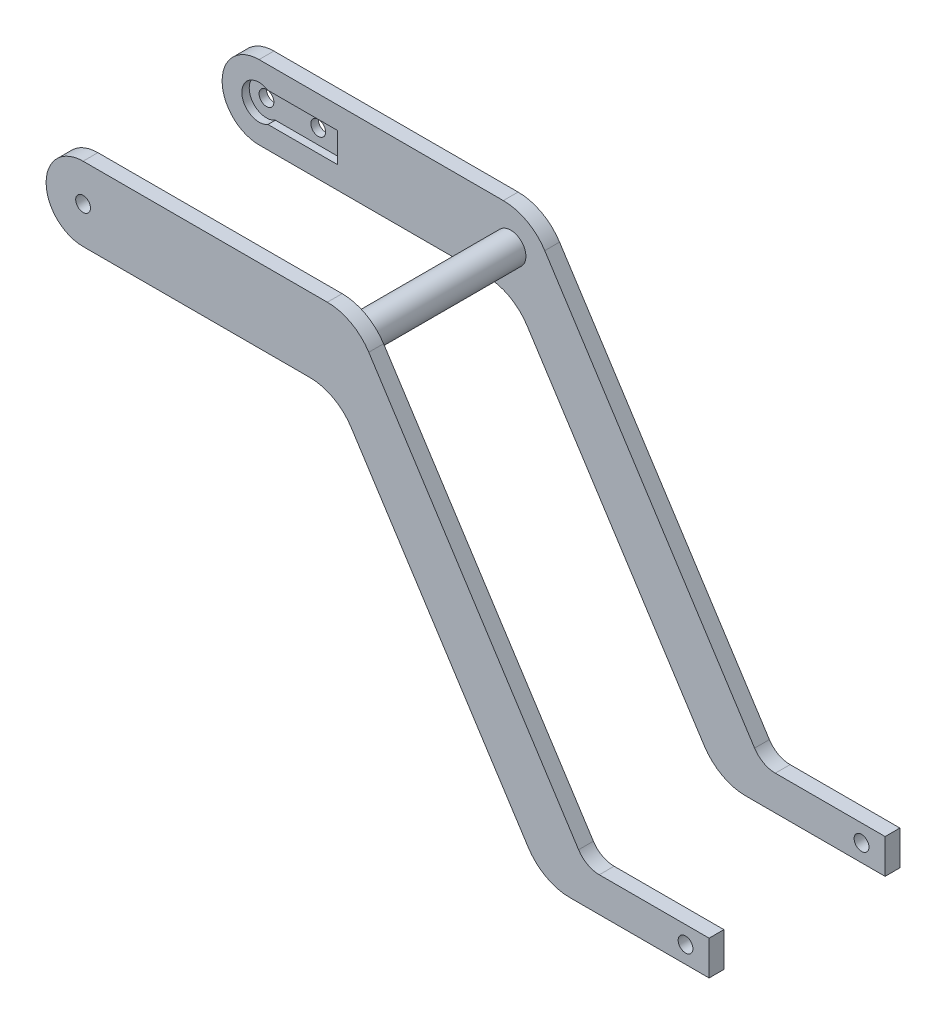
SolidWorks part; units mm, degrees
ref_plane "前基準面" through (0, 0, 0) normal (0, 0, 1) x (1, 0, 0)
ref_plane "上基準面" through (0, 0, 0) normal (0, 1, 0) x (1, 0, 0)
ref_plane "右基準面" through (0, 0, 0) normal (1, 0, 0) x (0, 0, -1)
sketch "草?" plane through (0, 0, 0) normal (0, 0, 1) x (1, 0, 0)
  line L0 (0, 0) -> (-0.115, 0)
  line L1 (0, -15) -> (2.1689, -15)
  line L3 (0, 0) -> (49.5442, 0)
  line L4 (2.1689, -15) -> (45.9764, -15)
  line L5 (54.3851, -19.5877) -> (90.317, -75.4123)
  line L6 (57.9529, -4.5877) -> (100.5105, -70.7062)
  line L7 (98.7257, -80) -> (126.9869, -80)
  line L8 (104.7148, -73) -> (126.9869, -73)
  line L9 (126.9869, -73) -> (126.9869, -80)
  arc A0 (0, 0) -> (0, -15) centre (0, -7.5) ccw
  arc A1 (49.5442, 0) -> (57.9529, -4.5877) centre (49.5442, -10) cw
  arc A2 (45.9764, -15) -> (54.3851, -19.5877) centre (45.9764, -25) cw
  arc A3 (90.317, -75.4123) -> (98.7257, -80) centre (98.7257, -70) ccw
  arc A4 (100.5105, -70.7062) -> (104.7148, -73) centre (104.7148, -68) ccw
  circle A5 centre (0, -7.5) radius 1.5
  point P13 (55, 0)
  point P22 (101.9869, -73)
  dimension "D1" = 15
  dimension "D2" = 3
  dimension "D6" = 10
  dimension "D7" = 10
  dimension "D8" = 10
  dimension "D9" = 5
  dimension "D3" = 55
  dimension "D4" = 25
  dimension "D5" = 7
  dimension "D10" = 65
extrude "填料-伸長1" add sketch "草?" along normal blind 3 contours A4 L6 A1 L3 A0 L1 L4 A2 L5 A3 L7 L9 L8 A5
sketch "草圖2" plane through (0, 0, 3) normal (0, 0, 1) x (1, 0, 0)
  line L0 (126.9869, -73) -> (126.9869, -80) construction
  circle A0 centre (122.2069, -76.5) radius 1.5
  point P2 (0, 0)
  point P3 (126.9869, -76.5)
  dimension "D1" = 3
  dimension "D2" = 4.78
extrude "除料-伸長1" cut sketch "草圖2" along normal blind 111.5 and the other way blind 41.5
sketch "草圖5" plane through (0, 0, 3) normal (0, 0, 1) x (1, 0, 0)
  line L0 (3.5, -7.5) -> (16, -7.5) construction
  line L2 (1.8028, -4.5) -> (15.9298, -4.5)
  line L3 (1.8028, -10.5) -> (15.9298, -10.5)
  line L4 (15.9298, -4.5) -> (15.9298, -10.5)
  arc A2 (1.8028, -4.5) -> (1.8028, -10.5) centre (0, -7.5) ccw
  dimension "D2" = 7
  dimension "D1" = 16
  dimension "D3" = 6
extrude "除料-伸長2" cut sketch "草圖5" against normal blind 1.5
sketch "草圖6" plane through (0, 0, 1.5) normal (0, 0, 1) x (1, 0, 0)
  line L0 (0, -7.5) -> (10.5, -7.5) construction
  circle A0 centre (10.5, -7.5) radius 1.5
  dimension "D2" = 3
  dimension "D1" = 10.5
extrude "除料-伸長3" cut sketch "草圖6" against normal through all
ref_plane "平面1" through (0, 0, 19.35) normal (0, 0, 1) x (1, 0, 0)
sketch "草圖8" plane through (0, 0, 3) normal (0, 0, 1) x (1, 0, 0)
  circle A1 centre (51.049, -7.5154) radius 3.075
  dimension "D1" = 6.15
extrude "填料-伸長3" add sketch "草圖8" along normal up to surface (16.35 mm away) up to plane "平面1"
mirror "鏡射7" about plane through (0, 0, 19.35) normal (0, 0, 1) of "填料-伸長3"
mirror "鏡射8" about plane through (0, 0, 19.35) normal (0, 0, 1) of "填料-伸長1", "鏡射7"
sketch "草圖11" plane through (0, 0, 35.7) normal (0, 0, -1) x (-1, 0, 0)
  circle A0 centre (-122.2069, -76.5) radius 1.5
extrude "除料-伸長4" cut sketch "草圖11" against normal blind 41.5
